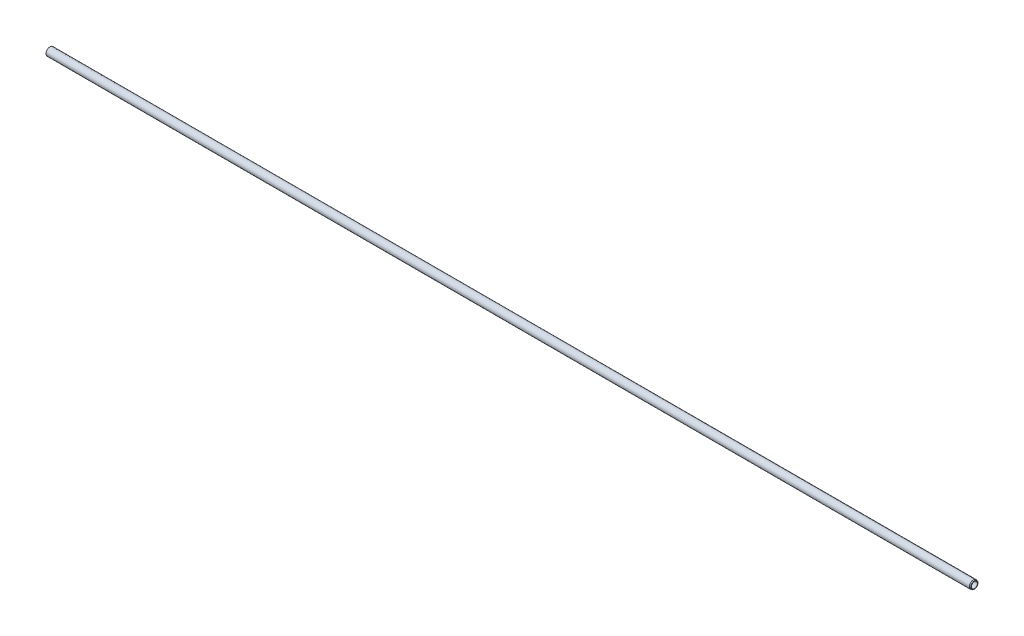
SolidWorks part; units mm, degrees
ref_plane "Front" through (0, 0, 0) normal (0, 0, 1) x (1, 0, 0)
ref_plane "Top" through (0, 0, 0) normal (0, 1, 0) x (1, 0, 0)
ref_plane "Right" through (0, 0, 0) normal (1, 0, 0) x (0, 0, -1)
sketch "Sketch1" plane through (0, 0, 0) normal (0, 0, 1) x (1, 0, 0)
  line L0 (0, 0) -> (1352.4571, 0) construction
  line L1 (0, 10) -> (0, 7.5)
  line L2 (0, 7.5) -> (2312, 7.5)
  line L4 (0, 10) -> (2309.5, 10)
  line L6 (2309.5, 10) -> (2312, 9.0901)
  line L7 (2312, 9.0901) -> (2312, 7.5)
  dimension "D1" = 20
  dimension "D2" = 15
  dimension "D3" = 20
  dimension "D6" = 2312
  dimension "D8" = 2.5
revolve "Base-Revolve" add sketch "Sketch1" angle 360 about L0
